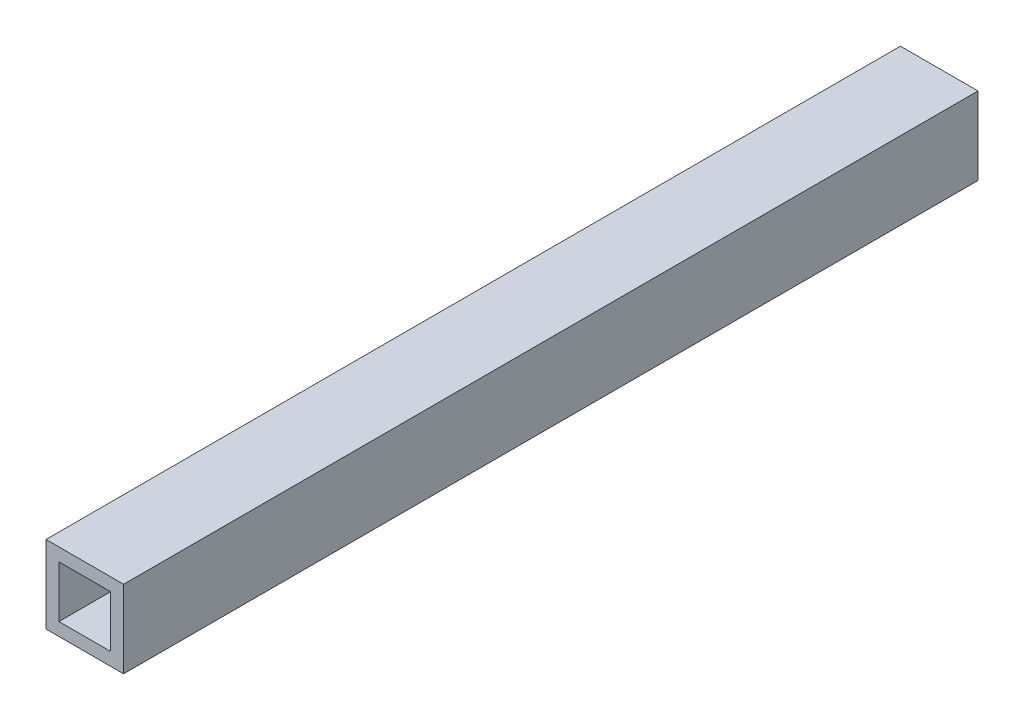
SolidWorks part; units mm, degrees
ref_plane "Front" through (0, 0, 0) normal (0, 0, 1) x (1, 0, 0)
ref_plane "Top" through (0, 0, 0) normal (0, 1, 0) x (1, 0, 0)
ref_plane "Right" through (0, 0, 0) normal (1, 0, 0) x (0, 0, -1)
sketch "Sketch1" plane through (0, 0, 0) normal (0, 0, 1) x (1, 0, 0)
  line L1 (-10.0135, 5.5766) -> (9.0365, 5.5766)
  line L2 (-10.0135, 5.5766) -> (-10.0135, -13.4734)
  line L3 (-10.0135, -13.4734) -> (9.0365, -13.4734)
  line L4 (9.0365, 5.5766) -> (9.0365, -13.4734)
  dimension "D1" = 19.05
  dimension "D2" = 19.05
extrude "Boss-Extrude1" add sketch "Sketch1" along normal blind 209.804
sketch "Sketch2" plane through (0, 0, 0) normal (0, 0, -1) x (-1, 0, 0)
  line L8 (6.8385, -10.2984) -> (6.8385, 2.4016)
  line L9 (6.8385, 2.4016) -> (-5.8615, 2.4016)
  line L10 (-5.8615, 2.4016) -> (-5.8615, -10.2984)
  line L11 (-5.8615, -10.2984) -> (6.8385, -10.2984)
  line L12 (6.8385, -10.2984) -> (6.8385, 2.4016)
  line L13 (6.8385, 2.4016) -> (-5.8615, 2.4016)
  line L14 (-5.8615, 2.4016) -> (-5.8615, -10.2984)
  line L15 (-5.8615, -10.2984) -> (6.8385, -10.2984)
  dimension "D1" = 3.175
extrude "Cut-Extrude1" cut sketch "Sketch2" against normal through all
